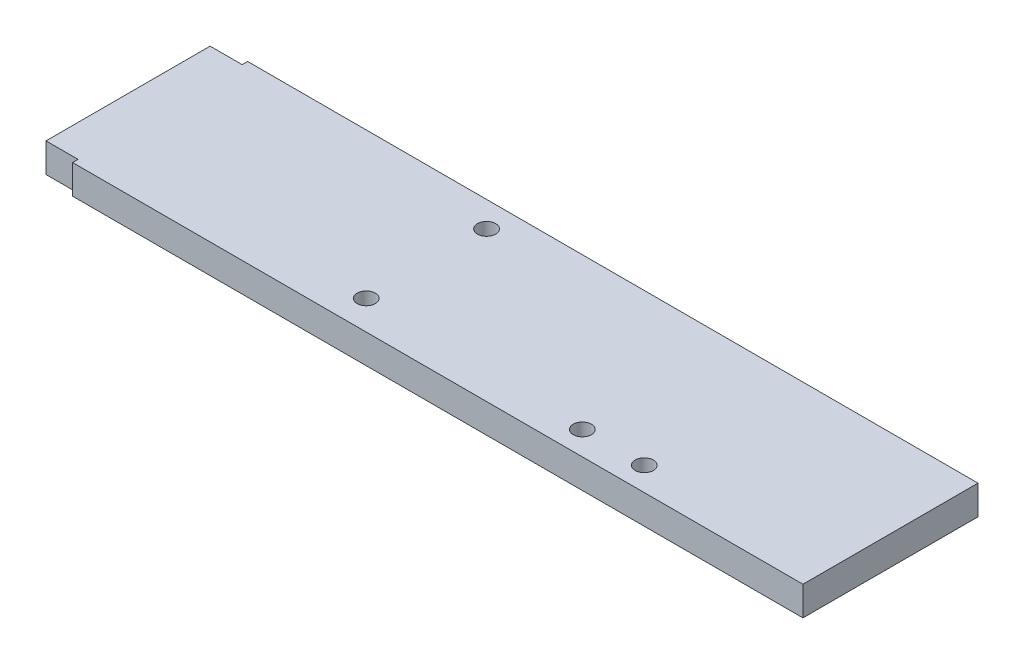
SolidWorks part; units mm, degrees
ref_plane "Front Plane" through (0, 0, 0) normal (0, 0, 1) x (1, 0, 0)
ref_plane "Top Plane" through (0, 0, 0) normal (0, 1, 0) x (1, 0, 0)
ref_plane "Right Plane" through (0, 0, 0) normal (1, 0, 0) x (0, 0, -1)
sketch "Sketch1" plane through (0, 0, 0) normal (0, 1, 0) x (1, 0, 0)
  line L4 (21.2513, -1.8101) -> (21.2513, -11.4101)
  line L5 (-20.5597, -11.1101) -> (-18.7997, -11.1101)
  line L6 (-20.5597, -11.1101) -> (-20.5597, -2.1101)
  line L7 (-20.5597, -2.1101) -> (-18.7997, -2.1101)
  line L8 (-18.7997, -2.1101) -> (-18.7997, -1.8101)
  line L9 (-18.7997, -11.1101) -> (-18.7997, -11.4101)
  line L10 (-18.7997, -11.4101) -> (21.2513, -11.4101)
  line L11 (-18.7997, -1.8101) -> (21.2513, -1.8101)
  line L12 (-18.7997, -11.4101) -> (-4.2997, -11.4101)
  line L13 (21.2513, -11.4101) -> (7.8513, -11.4101)
  line L14 (7.8513, -11.4101) -> (11.2513, -11.4101)
  circle A0 centre (-4.2997, -3.2101) radius 0.5
  circle A1 centre (-4.2997, -9.8101) radius 0.5
  circle A2 centre (7.8513, -10.1101) radius 0.5
  circle A3 centre (11.2513, -10.1101) radius 0.5
  point P19 (0, 0)
  point P20 (0, 0)
  point P21 (0, 0)
extrude "Boss-Extrude3" add sketch "Sketch1" along normal blind 1.6 contours L4 L10 L9 L5 L6 L7 L8 L11
sketch "Sketch2" plane through (0, 1.6, 0) normal (0, 1, 0) x (1, 0, 0)
  circle A0 centre (-4.2997, -3.2101) radius 0.5
  circle A1 centre (-4.2997, -9.8101) radius 0.5
  circle A2 centre (7.8513, -10.1101) radius 0.5
  circle A3 centre (11.2513, -10.1101) radius 0.5
  point P8 (0, 0)
  point P9 (0, 0)
  point P13 (0, 0)
  point P15 (0, 0)
  point P16 (0, 0)
  point P17 (-4.2989, -9.8101)
extrude "Cut-Extrude1" cut sketch "Sketch2" against normal through all and the other way through all
